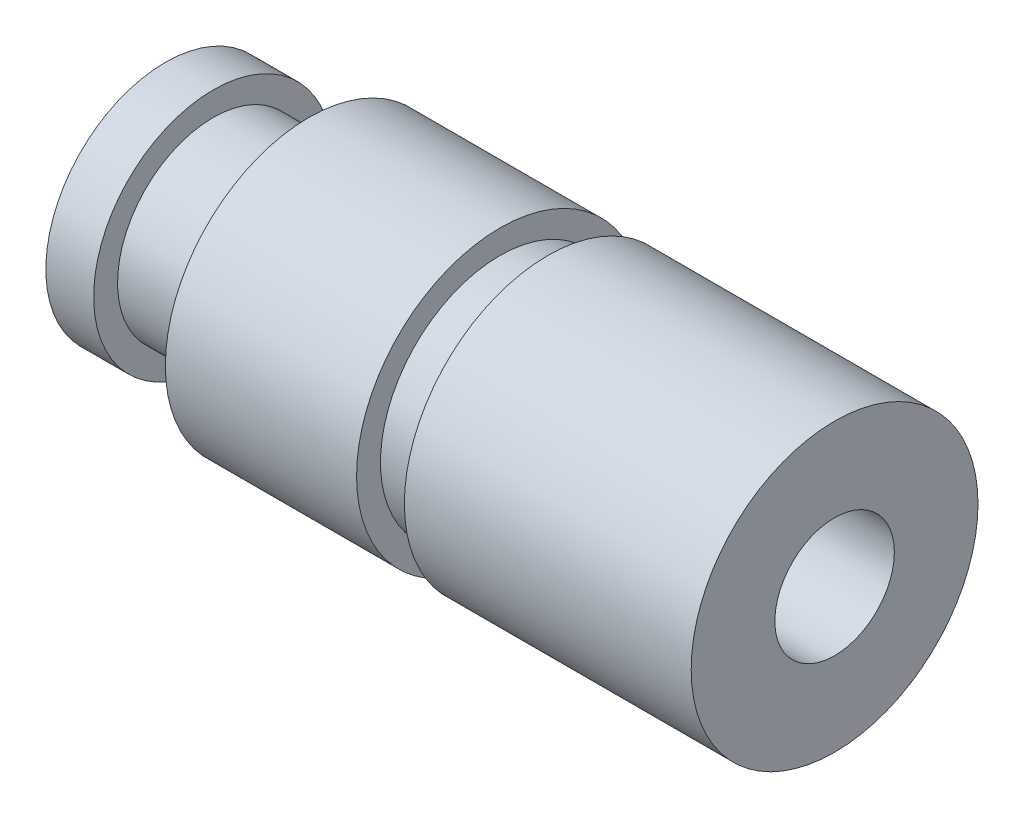
SolidWorks part; units mm, degrees
ref_plane "Face" through (0, 0, 0) normal (0, 0, 1) x (1, 0, 0)
ref_plane "Dessus" through (0, 0, 0) normal (0, 1, 0) x (1, 0, 0)
ref_plane "Droite" through (0, 0, 0) normal (1, 0, 0) x (0, 0, -1)
sketch "Esquisse1" plane through (0, 0, 0) normal (0, 0, 1) x (1, 0, 0)
  line L0 (0, 0) -> (0, 2.5)
  line L1 (0, 2.5) -> (1, 2.5)
  line L2 (1, 2.5) -> (1, 2)
  line L3 (3, 2) -> (3, 3)
  line L4 (3, 3) -> (14, 3)
  line L5 (14, 3) -> (14, 0)
  line L6 (14, 0) -> (0, 0)
  line L7 (1, 2) -> (3, 2)
  dimension "D1" = 2.5
  dimension "D2" = 1
  dimension "D3" = 2
  dimension "D4" = 2
  dimension "D5" = 3
  dimension "D6" = 14
revolve "Révolution1" add sketch "Esquisse1" angle 360 about L6
hole_wizard "Trou taraudé M31" positions "Esquisse3" profile "Esquisse2" tap size "M3" standard "ISO"
sketch "Esquisse3" plane through (14, 0, 0) normal (1, 0, 0) x (0, 0, -1)
  circle A0 centre (0, 0) radius 3 construction
  point P0 (0, 0)
sketch "Esquisse2" plane through (14, 0, 0) normal (0, 1, 0) x (0, 0, -1)
  line L0 (0, 0) -> (0, 9.2511)
  line L1 (0, 9.2511) -> (1.25, 8.5)
  line L2 (1.25, 8.5) -> (1.25, 0)
  line L5 (1.25, 0) -> (0, 0)
  line L10 (0, 9.2511) -> (-1.25, 8.5) construction
  line L11 (0, -6.35) -> (0, 107.95) construction
  dimension "Diamètre du trou pour taraudage" = 2.5
  dimension "Profondeur du trou pour taraudage" = 8.5
  dimension "Angle de pointe" = 118
cosmetic thread "Filetage de perçage1" parameters "D1"=6, "D2"=3
ref_plane "Plan1" through (7.5, 0, 0) normal (-1, 0, 0) x (0, 0, 1)
sketch "Esquisse4" plane through (7.5, 0, 0) normal (-1, 0, 0) x (0, 0, 1)
  circle A0 centre (0, 0) radius 3 construction
  circle A1 centre (0, 0) radius 3
  circle A2 centre (0, 0) radius 2.5
  dimension "D1" = 5
extrude "Enlèv. mat.-Extru.1" cut sketch "Esquisse4" against normal mid plane 1
